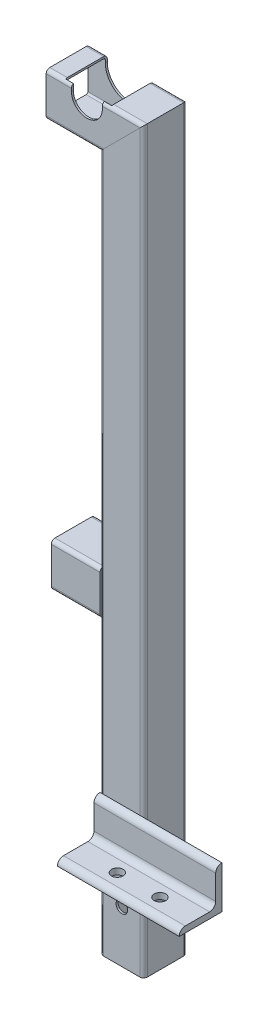
SolidWorks part; units mm, degrees
ref_plane "Front Plane" through (0, 0, 0) normal (0, 0, 1) x (1, 0, 0)
ref_plane "Top Plane" through (0, 0, 0) normal (0, 1, 0) x (1, 0, 0)
ref_plane "Right Plane" through (0, 0, 0) normal (1, 0, 0) x (0, 0, -1)
sketch "Sketch1" plane through (0, 0, 0) normal (0, 0, 1) x (1, 0, 0)
  line L0 (228.7, 0) -> (228.7, 509)
  line L1 (228.7, 509) -> (166.6, 509)
  line L2 (228.7, 0) -> (228.7, -80)
  line L3 (228.7, 176.5) -> (170.8, 176.5)
  dimension "D1" = 509
  dimension "D2" = 80
  dimension "D3" = 62.1
  dimension "D4" = 228.7
  dimension "D5" = 176.5
  dimension "D6" = 57.9
other "Structural MemberMain"
ref_plane "Plane1" through (228.7, 0, 0) normal (0, 1, 0) x (-1, 0, 0)
sketch "Sketch11" plane through (228.7, 0, 0) normal (0, 1, 0) x (-1, 0, 0)
  line L0 (-14.9, 16.3) -> (14.9, 16.3)
  line L1 (-14.9, 17.9) -> (14.9, 17.9)
  line L2 (-17.9, 14.9) -> (-17.9, -14.9)
  line L3 (-14.9, -17.9) -> (14.9, -17.9)
  line L4 (17.9, 14.9) -> (17.9, -14.9)
  line L5 (-17.9, 17.9) -> (17.9, -17.9) construction
  line L6 (-17.9, -17.9) -> (17.9, 17.9) construction
  line L7 (16.3, 14.9) -> (16.3, -14.9)
  line L8 (-14.9, -16.3) -> (14.9, -16.3)
  line L9 (-16.3, 14.9) -> (-16.3, -14.9)
  arc A0 (-17.9, -14.9) -> (-14.9, -17.9) centre (-14.9, -14.9) ccw
  arc A1 (14.9, -17.9) -> (17.9, -14.9) centre (14.9, -14.9) ccw
  arc A2 (17.9, 14.9) -> (14.9, 17.9) centre (14.9, 14.9) ccw
  arc A3 (-14.9, 17.9) -> (-17.9, 14.9) centre (-14.9, 14.9) ccw
  arc A4 (16.3, 14.9) -> (14.9, 16.3) centre (14.9, 14.9) ccw
  arc A5 (14.9, -16.3) -> (16.3, -14.9) centre (14.9, -14.9) ccw
  arc A6 (-16.3, -14.9) -> (-14.9, -16.3) centre (-14.9, -14.9) ccw
  arc A7 (-14.9, 16.3) -> (-16.3, 14.9) centre (-14.9, 14.9) ccw
  point P0 (0, 0)
  point P30 (0, 0)
  dimension "D3" = 3
  dimension "D1" = 35.8
  dimension "D2" = 35.8
  dimension "D4" = 1.6
sketch "Sketch12" plane through (0, 0, 0) normal (0, 0, 1) x (1, 0, 0)
  line L1 (200, 521.7) -> (200, 532.1) construction
  line L2 (187.3, 521.7) -> (187.3, 532.1)
  line L3 (212.7, 521.7) -> (212.7, 532.1)
  line L4 (228.7, 509) -> (166.6, 509) construction
  line L5 (166.6, 526.9) -> (246.6, 526.9) construction
  arc A0 (187.3, 521.7) -> (212.7, 521.7) centre (200, 521.7) ccw
  arc A1 (212.7, 532.1) -> (187.3, 532.1) centre (200, 532.1) ccw
  point P2 (200, 526.9)
  dimension "D1" = 25.4
  dimension "D2" = 200
extrude "Cut-ExtrudeTopRailGuide" cut sketch "Sketch12" against normal through all and the other way through all
sketch "Sketch13" plane through (0, 0, 0) normal (0, 1, 0) x (1, 0, 0)
  line L0 (210.8, -17.9) -> (310.8, -17.9)
  line L1 (212.7, -17.9) -> (243.6, -17.9) construction
  line L2 (210.8, -14.9) -> (210.8, 14.9) construction
  point P4 (260.8, -17.9)
  dimension "D1" = 100
other "Structural MemberAngle"
ref_plane "Plane2" through (210.8, 0, 17.9) normal (1, 0, 0) x (0, 1, 0)
sketch "Sketch14" plane through (210.8, 0, 17.9) normal (1, 0, 0) x (0, 1, 0)
  line L0 (0, 0) -> (0, 35)
  line L1 (0, 17.5) -> (5, 17.5) construction
  line L2 (5, 30) -> (5, 10)
  line L3 (10, 5) -> (30, 5)
  line L4 (17.5, 5) -> (17.5, 0) construction
  line L5 (35, 0) -> (0, 0)
  arc A0 (35, 0) -> (30, 5) centre (30, 0) ccw
  arc A1 (0, 35) -> (5, 30) centre (0, 30) cw
  arc A2 (10, 5) -> (5, 10) centre (10, 10) cw
  point P10 (17.5, 0)
  point P14 (0, 17.5)
  point P15 (5, 17.5)
  point P16 (17.5, 5)
  point P17 (5, 35)
  point P18 (35, 5)
  point P21 (0, 0)
  dimension "D2" = 5
  dimension "D3" = 35
  dimension "Radius_1" = 5
  dimension "D1" = 5
sketch "Sketch15" plane through (0, 0, 0) normal (0, 1, 0) x (1, 0, 0)
  line L0 (260.8, -17.9) -> (260.8, -52.9) construction
  line L1 (310.8, -52.9) -> (210.8, -52.9) construction
  line L2 (-65.8005, -37.9) -> (587.4005, -37.9) construction
  line L3 (210.8, -17.9) -> (310.8, -17.9) construction
  line L4 (0, 28.933) -> (0, -28.933) construction
  circle A0 centre (179.8, -37.9) radius 4.7625 construction
  circle A1 centre (215.6, -37.9) radius 5.0441 construction
  circle A2 centre (245, -37.9) radius 4.7625
  circle A3 centre (280, -37.9) radius 4.7625
  point P7 (260.8, -37.9)
  point P16 (0, 0)
  dimension "D2" = 9.525
  dimension "D1" = 20
  dimension "D3" = 215.6
  dimension "D4" = 35.8
  dimension "D5" = 35
  dimension "D6" = 280
extrude "Cut-ExtrudeMountingHoles" cut sketch "Sketch15" along normal through all
sketch "Sketch16" plane through (0, 0, 0) normal (0, 0, 1) x (1, 0, 0)
  line L4 (219.05, 521.7) -> (219.05, 532.1)
  line L5 (180.95, 532.1) -> (180.95, 521.7)
  line L6 (219.05, 521.7) -> (219.05, 532.1)
  line L7 (180.95, 532.1) -> (180.95, 521.7)
  arc A4 (180.95, 521.7) -> (219.05, 521.7) centre (200, 521.7) ccw
  arc A5 (219.05, 532.1) -> (180.95, 532.1) centre (200, 532.1) ccw
  arc A6 (180.95, 521.7) -> (219.05, 521.7) centre (200, 521.7) ccw
  arc A7 (219.05, 532.1) -> (180.95, 532.1) centre (200, 532.1) ccw
  dimension "D1" = 6.35
extrude "Cut-ExtrudeEnlargeRailGuide" cut sketch "Sketch16" against normal through all and the other way up to surface
sketch "Sketch17" plane through (0, 0, 17.9) normal (0, 0, 1) x (1, 0, 0)
  line L0 (228.7, 0) -> (228.7, -80) construction
  line L1 (210.8, 0) -> (310.8, 0) construction
  line L2 (246.6, 0) -> (246.6, -80) construction
  circle A0 centre (228.7, -37.5) radius 4.7625
  dimension "D1" = 9.525
  dimension "D3" = 17.9
  dimension "D2" = 37.5
extrude "Cut-Extrude1" cut sketch "Sketch17" against normal through all
